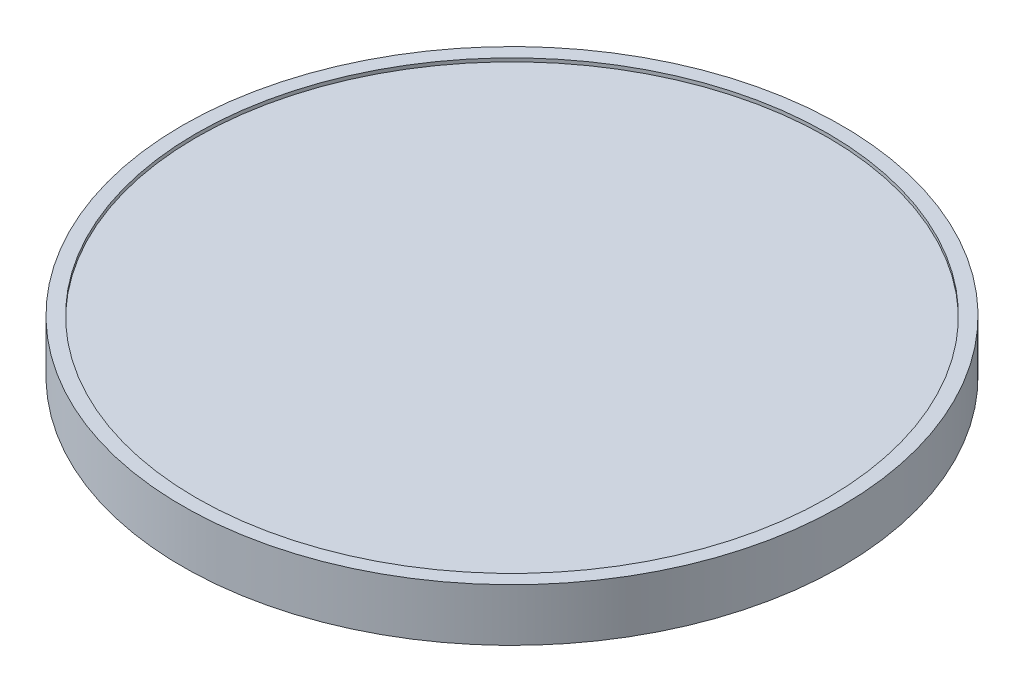
SolidWorks part; units mm, degrees
material "Copper"
ref_plane "Front Plane" through (0, 0, 0) normal (0, 0, 1) x (1, 0, 0)
ref_plane "Top Plane" through (0, 0, 0) normal (0, 1, 0) x (1, 0, 0)
ref_plane "Right Plane" through (0, 0, 0) normal (1, 0, 0) x (0, 0, -1)
sketch "Sketch1" plane through (0, 0, 0) normal (0, 0, 1) x (1, 0, 0)
  line L0 (0, 0.66) -> (9.125, 0.66)
  line L1 (9.125, 0.66) -> (9.125, 0.76)
  line L2 (9.125, 0.76) -> (9.525, 0.76)
  line L3 (9.525, 0.76) -> (9.525, -0.76)
  line L4 (9.525, -0.76) -> (9.125, -0.76)
  line L5 (9.125, -0.76) -> (9.125, -0.66)
  line L6 (9.125, -0.66) -> (0, -0.66)
  line L7 (0, -0.66) -> (0, 0.66)
  line L8 (0, 5.732) -> (0, -3.3265) construction
  point P3 (0, 0)
  point P9 (9.525, 0)
  dimension "D1" = 1.32
  dimension "D2" = 1.52
  dimension "D3" = 19.05
  dimension "D4" = 18.25
revolve "Revolve1" add sketch "Sketch1" angle 360 about L8
